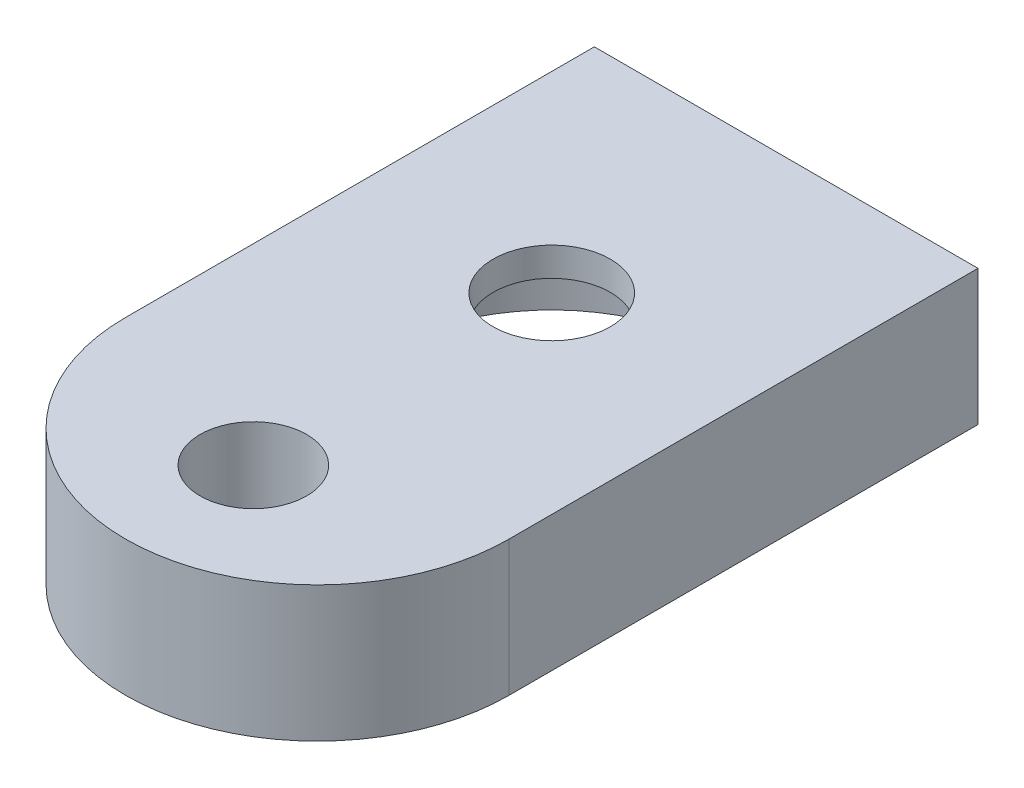
SolidWorks part; units mm, degrees
ref_plane "Front Plane" through (0, 0, 0) normal (0, 0, 1) x (1, 0, 0)
ref_plane "Top Plane" through (0, 0, 0) normal (0, 1, 0) x (1, 0, 0)
ref_plane "Right Plane" through (0, 0, 0) normal (1, 0, 0) x (0, 0, -1)
sketch "Sketch1" plane through (0, 0, 0) normal (0, 1, 0) x (1, 0, 0)
  line L9 (9, 11) -> (-9, 11)
  line L10 (9, 11) -> (-9, 11)
  line L11 (9, -11) -> (9, 11)
  line L16 (9, -11) -> (9, 11)
  line L17 (-9, 11) -> (-9, -11)
  line L18 (-9, 11) -> (-9, -11)
  arc A2 (-9, -11) -> (9, -11) centre (0, -11) ccw
  arc A3 (-9, -11) -> (9, -11) centre (0, -11) ccw
  dimension "D1" = 0
extrude "Boss-Extrude1" add sketch "Sketch1" along normal blind 6.35
sketch "Sketch2" plane through (0, 0, 0) normal (0, -1, 0) x (1, 0, 0)
  circle A0 centre (0, 0) radius 8 construction
  circle A1 centre (0, 0) radius 8
extrude "Cut-Extrude1" cut sketch "Sketch2" against normal blind 5
sketch "Sketch3" plane through (0, 5, 0) normal (0, -1, 0) x (1, 0, 0)
  circle A0 centre (0, 0) radius 2.75 construction
  circle A1 centre (0, 0) radius 2.75
extrude "Cut-Extrude2" cut sketch "Sketch3" against normal through all
sketch "Sketch4" plane through (0, 0, 0) normal (0, -1, 0) x (1, 0, 0)
  circle A0 centre (0, 14) radius 2.5 construction
  circle A1 centre (0, 14) radius 2.5
  circle A2 centre (0, -13.5) radius 2.5 construction
  circle A3 centre (0, -13.5) radius 2.5
extrude "Cut-Extrude3" cut sketch "Sketch4" against normal through all
